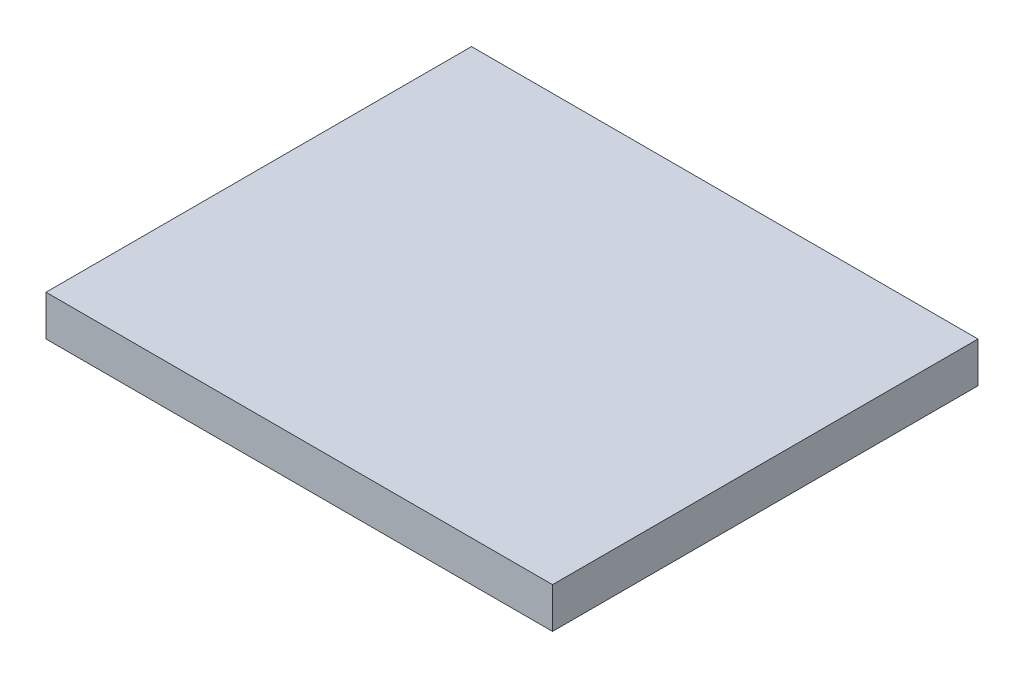
SolidWorks part; units mm, degrees
ref_plane "Front Plane" through (0, 0, 0) normal (0, 0, 1) x (1, 0, 0)
ref_plane "Top Plane" through (0, 0, 0) normal (0, 1, 0) x (1, 0, 0)
ref_plane "Right Plane" through (0, 0, 0) normal (1, 0, 0) x (0, 0, -1)
sketch "Sketch1" plane through (0, 0, 0) normal (0, 1, 0) x (1, 0, 0)
  line L2 (-185, 350) -> (-185, -183.4)
  line L4 (450, 350) -> (450, -183.4)
  line L5 (450, -183.4) -> (-185, -183.4)
  line L6 (450, 350) -> (-185, 350)
  dimension "D1" = 533.4
  dimension "D2" = 635
extrude "Boss-Extrude1" add sketch "Sketch1" along normal blind 50.8
ref_plane "Plane1" through (-185, 0, 183.4) normal (1, 0, 0) x (0, 0, -1)
